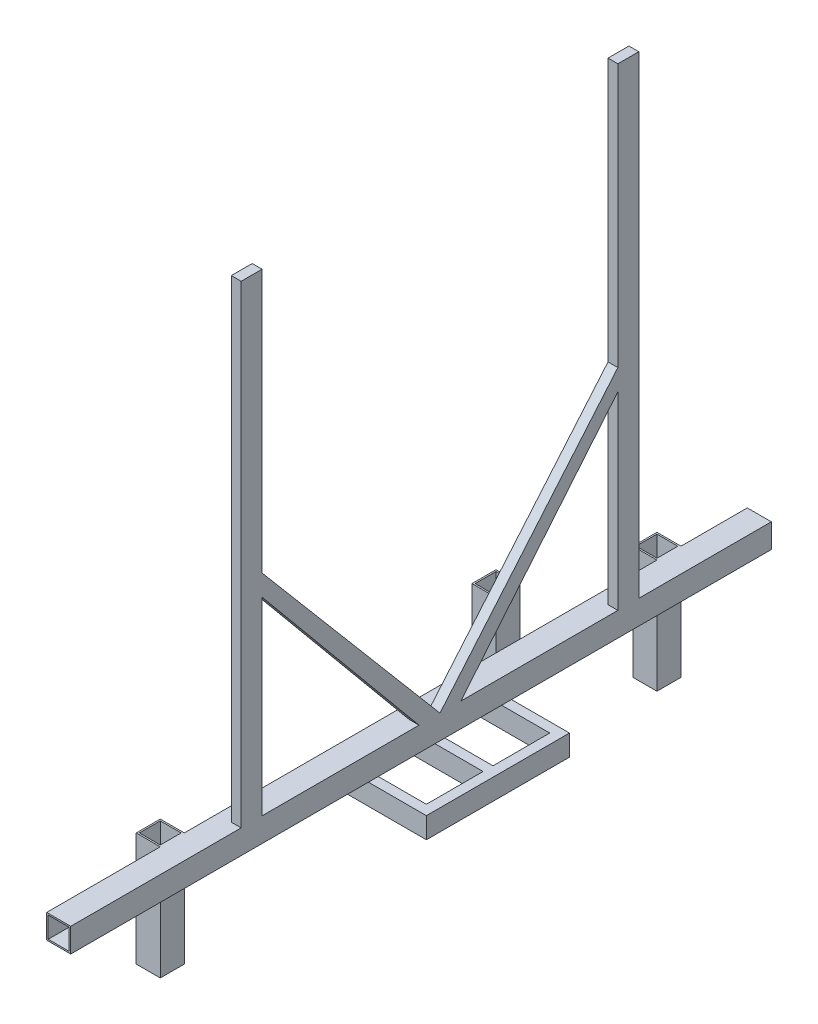
SolidWorks part; units mm, degrees
ref_plane "Front Plane" through (0, 0, 0) normal (0, 0, 1) x (1, 0, 0)
ref_plane "Top Plane" through (0, 0, 0) normal (0, 1, 0) x (1, 0, 0)
ref_plane "Right Plane" through (0, 0, 0) normal (1, 0, 0) x (0, 0, -1)
sketch "Sketch1" plane through (0, 0, 0) normal (0, 0, 1) x (1, 0, 0)
  line L1 (-11.049, -11.049) -> (11.049, -11.049)
  line L2 (-11.049, -11.049) -> (-11.049, 11.049)
  line L3 (-11.049, 11.049) -> (11.049, 11.049)
  line L4 (11.049, -11.049) -> (11.049, 11.049)
  line L5 (-11.049, -11.049) -> (11.049, 11.049) construction
  line L6 (-11.049, 11.049) -> (11.049, -11.049) construction
  line L7 (-12.7, -12.7) -> (12.7, -12.7)
  line L8 (-12.7, -12.7) -> (-12.7, 12.7)
  line L9 (-12.7, 12.7) -> (12.7, 12.7)
  line L10 (12.7, -12.7) -> (12.7, 12.7)
  line L11 (-12.7, -12.7) -> (12.7, 12.7) construction
  line L12 (-12.7, 12.7) -> (12.7, -12.7) construction
  point P0 (0, 0)
  point P6 (0, 0)
  point P11 (11.049, 0)
  dimension "D1" = 25.4
  dimension "D2" = 22.098
extrude "Boss-Extrude1" add sketch "Sketch1" along normal mid plane 740
sketch "Sketch2" plane through (0, 12.7, 0) normal (0, 1, 0) x (1, 0, 0)
  line L0 (12.7, -370) -> (12.7, 370) construction
  line L1 (12.7, -167.902) -> (2.286, -167.902)
  line L2 (12.7, -167.902) -> (12.7, -190)
  line L3 (12.7, -190) -> (2.286, -190)
  line L4 (2.286, -167.902) -> (2.286, -190)
  line L5 (12.7, -370) -> (-12.7, -370) construction
  line L6 (12.7, 230) -> (2.286, 230)
  line L7 (2.286, 230) -> (2.286, 207.902)
  line L8 (12.7, 207.902) -> (2.286, 207.902)
  line L9 (12.7, 230) -> (12.7, 207.902)
  dimension "D1" = 180
  dimension "D2" = 22.098
  dimension "D3" = 10.414
  dimension "D5" = 420
  dimension "D4" = 2
extrude "Boss-Extrude2" add sketch "Sketch2" along normal blind 500
sketch "Sketch3" plane through (0, 0, 167.902) normal (0, 0, -1) x (-1, 0, 0)
  line L0 (-2.286, 512.7) -> (-2.286, 12.7) construction
  line L1 (-2.286, 234.798) -> (-12.7, 234.798)
  line L2 (-2.286, 234.798) -> (-2.286, 212.7)
  line L3 (-2.286, 212.7) -> (-12.7, 212.7)
  line L4 (-12.7, 234.798) -> (-12.7, 212.7)
  line L5 (-12.7, 512.7) -> (-12.7, 12.7) construction
  line L6 (-12.7, 12.7) -> (-2.286, 12.7) construction
  dimension "D1" = 200
  dimension "D2" = 22.098
sketch "Sketch4" plane through (0, 12.7, 0) normal (0, 1, 0) x (1, 0, 0)
  line L0 (12.7, -167.902) -> (12.7, 207.902) construction
  line L3 (2.286, -167.902) -> (2.286, 207.902) construction
  line L4 (2.286, 20) -> (12.7, 20)
  line L5 (2.286, 20) -> (2.286, -2.098)
  line L6 (2.286, -2.098) -> (12.7, -2.098)
  line L7 (12.7, 20) -> (12.7, -2.098)
  dimension "D1" = 22.098
sketch3d "3DSketch3"
  line L0 (2.286, 234.798, 167.902) -> (12.7, 212.7, 167.902) construction
  line L1 (12.7, 212.7, 167.902) -> (2.286, 212.7, 167.902) construction
  line L2 (2.286, 212.7, 167.902) -> (12.7, 234.798, 167.902) construction
  line L3 (2.286, 12.7, 2.098) -> (12.7, 12.7, -20) construction
  line L4 (12.7, 12.7, -20) -> (2.286, 12.7, -20) construction
  line L5 (2.286, 12.7, -20) -> (12.7, 12.7, 2.098) construction
  line L6 (7.493, 12.7, -8.951) -> (7.493, 223.749, 167.902)
loft "Loft3" add profiles "Sketch3", "Sketch4"
ref_plane "Plane4" through (0, 0, -20) normal (0, 0, 1) x (1, 0, 0)
mirror "Mirror2" about plane through (0, 0, -20) normal (0, 0, 1) of "Loft3"
sketch "Sketch11" plane through (0, -12.7, 0) normal (0, -1, 0) x (1, 0, 0)
  line L0 (-12.7, 370) -> (-12.7, -370) construction
  line L1 (-12.7, -14.793) -> (63.5, -14.793)
  line L2 (-12.7, -14.793) -> (-12.7, -25.207)
  line L3 (-12.7, -25.207) -> (63.5, -25.207)
  line L4 (63.5, -14.793) -> (63.5, -25.207)
  line L5 (63.5, -20) -> (-12.7, -20) construction
  line L7 (-12.7, 370) -> (-12.7, -370) construction
  line L8 (-12.7, 45.151) -> (63.5, 45.151)
  line L9 (-12.7, 45.151) -> (-12.7, 55.565)
  line L10 (-12.7, 55.565) -> (63.5, 55.565)
  line L11 (63.5, 45.151) -> (63.5, 55.565)
  line L12 (5.7277, -20) -> (-5.7277, -20) construction
  line L13 (-12.7, -85.151) -> (63.5, -85.151)
  line L14 (-12.7, -85.151) -> (-12.7, -95.565)
  line L15 (-12.7, -95.565) -> (63.5, -95.565)
  line L16 (63.5, -85.151) -> (63.5, -95.565)
  dimension "D1" = 10.414
  dimension "D2" = 76.2
  dimension "D3" = 59.944
  dimension "D4" = 59.944
extrude "Boss-Extrude3" add sketch "Sketch11" along normal blind 22.098
sketch "Sketch13" plane through (63.5, 0, 0) normal (1, 0, 0) x (0, 0, -1)
  line L1 (95.565, -12.7) -> (-55.565, -12.7)
  line L2 (95.565, -12.7) -> (95.565, -34.798)
  line L3 (95.565, -34.798) -> (-55.565, -34.798)
  line L4 (-55.565, -12.7) -> (-55.565, -34.798)
extrude "Boss-Extrude4" add sketch "Sketch13" along normal blind 10.414
sketch "Sketch14" plane through (0, 12.7, 0) normal (0, 1, 0) x (1, 0, 0)
  line L10 (12.7, -370) -> (-12.7, -370) construction
  line L11 (12.7, 370) -> (-12.7, 370) construction
  line L14 (0, -370) -> (0, 370) construction
  line L27 (-36.449, -226.251) -> (-14.351, -248.349) construction
  line L28 (-36.449, -248.349) -> (-14.351, -226.251) construction
  line L29 (-12.7, -250) -> (-38.1, -224.6) construction
  line L30 (-14.351, -248.349) -> (-14.351, -226.251)
  line L31 (-36.449, -226.251) -> (-14.351, -226.251)
  line L32 (-36.449, -248.349) -> (-36.449, -226.251)
  line L33 (-36.449, -248.349) -> (-14.351, -248.349)
  line L34 (-38.1, -250) -> (-38.1, -224.6)
  line L35 (-12.7, -224.6) -> (-38.1, -224.6)
  line L36 (-12.7, -250) -> (-12.7, -224.6)
  line L37 (-12.7, -250) -> (-38.1, -250)
  line L38 (-36.449, 298.349) -> (-14.351, 276.251) construction
  line L39 (-36.449, 276.251) -> (-14.351, 298.349) construction
  line L40 (-12.7, 274.6) -> (-38.1, 300) construction
  line L41 (-14.351, 276.251) -> (-14.351, 298.349)
  line L42 (-36.449, 298.349) -> (-14.351, 298.349)
  line L43 (-36.449, 276.251) -> (-36.449, 298.349)
  line L44 (-36.449, 276.251) -> (-14.351, 276.251)
  line L45 (-38.1, 274.6) -> (-38.1, 300)
  line L46 (-12.7, 300) -> (-38.1, 300)
  line L47 (-12.7, 274.6) -> (-12.7, 300)
  line L48 (-12.7, 274.6) -> (-38.1, 274.6)
  point P51 (-25.4, -237.3)
  point P74 (-25.4, 287.3)
extrude "Boss-Extrude5" add sketch "Sketch14" against normal blind 120
sketch "Sketch15" plane through (0, 12.7, 0) normal (0, 1, 0) x (1, 0, 0)
  line L0 (-12.7, -224.6) -> (-12.7, 274.6) construction
  line L1 (-12.7, 130) -> (-38.1, 130)
  line L2 (-12.7, 130) -> (-12.7, 104.6)
  line L3 (-12.7, 104.6) -> (-38.1, 104.6)
  line L4 (-38.1, 130) -> (-38.1, 104.6)
  line L5 (-38.1, 130) -> (-12.7, 104.6) construction
  line L7 (-14.351, 128.349) -> (-36.449, 128.349)
  line L8 (-14.351, 128.349) -> (-14.351, 106.251)
  line L9 (-14.351, 106.251) -> (-36.449, 106.251)
  line L10 (-36.449, 128.349) -> (-36.449, 106.251)
  line L11 (-14.351, 128.349) -> (-36.449, 106.251) construction
  line L12 (-14.351, 106.251) -> (-36.449, 128.349) construction
  point P7 (-25.4, 117.3)
  dimension "D1" = 25.4
  dimension "D2" = 25.4
  dimension "D3" = 240
  dimension "D4" = 22.098
extrude "Boss-Extrude6" add sketch "Sketch15" along normal blind 50.8 and the other way blind 25.4 separate body
